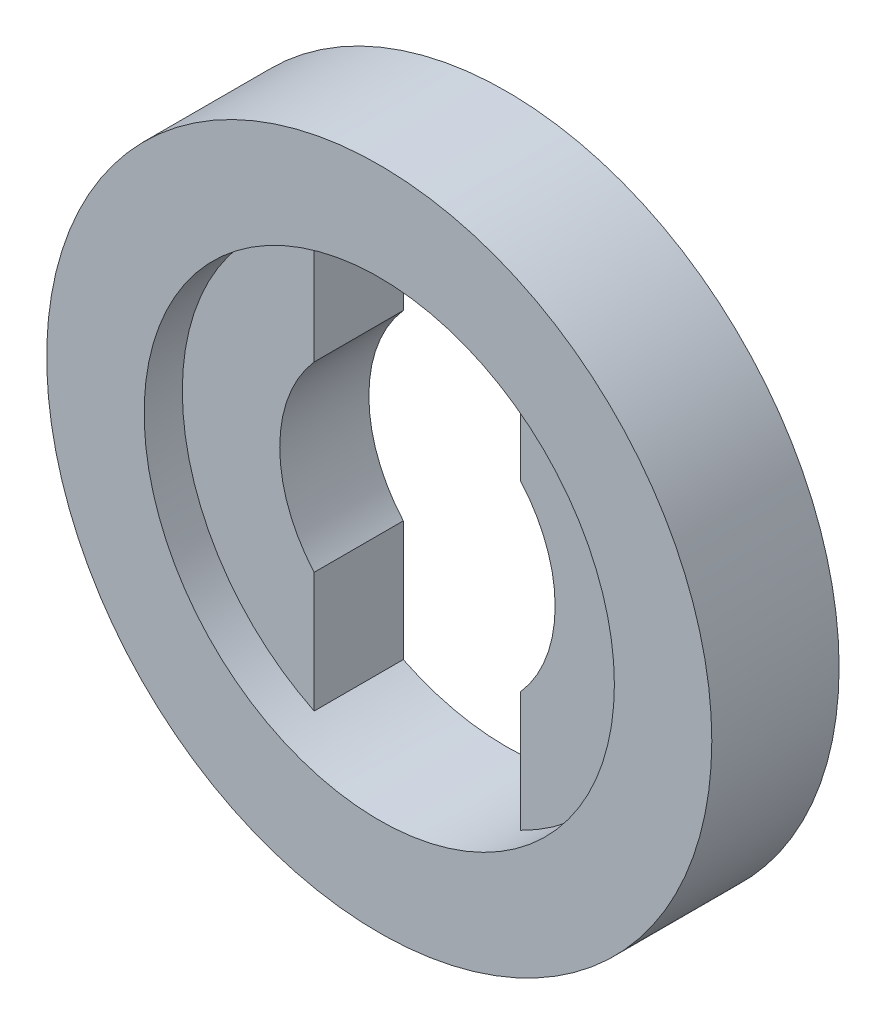
SolidWorks part; units mm, degrees
ref_plane "Front Plane" through (0, 0, 0) normal (0, 0, 1) x (1, 0, 0)
ref_plane "Top Plane" through (0, 0, 0) normal (0, 1, 0) x (1, 0, 0)
ref_plane "Right Plane" through (0, 0, 0) normal (1, 0, 0) x (0, 0, -1)
sketch "Sketch1" plane through (0, 0, 0) normal (0, 0, 1) x (1, 0, 0)
  line L0 (-1.3462, 0) -> (-3.2512, 0) construction
  line L1 (-2.2987, 0) -> (-2.2987, 3.2261) construction
  circle A0 centre (0, 0) radius 3.2512
  circle A1 centre (0, 0) radius 2.2987 construction
  circle A2 centre (0, 0) radius 1.3462
  dimension "D1" = 2.6924
  dimension "D2" = 6.5024
extrude "Extrude1" add sketch "Sketch1" along normal mid plane 1.2446
sketch "Sketch2" plane through (0, 0, 0.6223) normal (0, 0, 1) x (1, 0, 0)
  circle A0 centre (0, 0) radius 2.2987 construction
  circle A1 centre (0, 0) radius 2.2987
extrude "Cut-Extrude1" cut sketch "Sketch2" against normal blind 0.3734
sketch "Sketch3" plane through (0, 0, 0.2489) normal (0, 0, 1) x (1, 0, 0)
  line L0 (-1.0096, 2.0651) -> (-1.0096, 0.8904)
  line L1 (1.0096, 2.0651) -> (1.0096, 0.8904)
  line L2 (0, 0) -> (0, 2.2987) construction
  circle A0 centre (0, 0) radius 1.3462 construction
  circle A1 centre (0, 0) radius 2.2987 construction
  arc A2 (1.0096, 0.8904) -> (-1.0096, 0.8904) centre (0, 0) ccw
  arc A3 (1.0096, 2.0651) -> (-1.0096, 2.0651) centre (0, 0) ccw
  dimension "D1" = 2.0193
extrude "Cut-Extrude2" cut sketch "Sketch3" against normal through all
pattern_circular "CirPattern1" count 2 over 360 about axis through (0, 0, 0.6223) along (0, 0, -1) of "Cut-Extrude2"
equation "\"D1@Cut-Extrude1\" = \"thickness@Extrude1\"*.3"
equation "\"D1@Sketch3\"=\"D1@Sketch1\"*.75"
